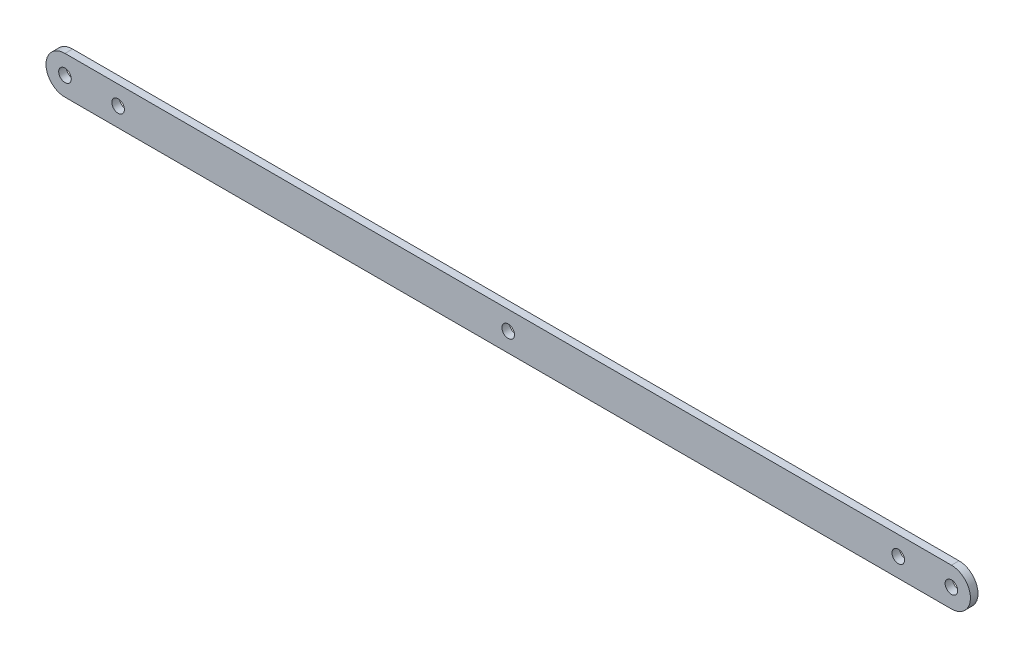
SolidWorks part; units mm, degrees
ref_plane "Přední rovina" through (0, 0, 0) normal (0, 0, 1) x (1, 0, 0)
ref_plane "Horní rovina" through (0, 0, 0) normal (0, 1, 0) x (1, 0, 0)
ref_plane "Pravá rovina" through (0, 0, 0) normal (1, 0, 0) x (0, 0, -1)
sketch "Skica1" plane through (0, 0, 0) normal (0, 0, 1) x (1, 0, 0)
  line L0 (0, 12.5) -> (584, 12.5)
  line L1 (0, -12.5) -> (584, -12.5)
  line L2 (0, 12.5) -> (0, -12.5) construction
  line L3 (584, -12.5) -> (584, 12.5) construction
  line L4 (-12.5, 0) -> (596.5, 0) construction
  line L5 (35, 4.15) -> (35, -4.15) construction
  line L6 (292, 4.15) -> (292, -4.15) construction
  line L7 (549, 4.15) -> (549, -4.15) construction
  arc A0 (0, 12.5) -> (0, -12.5) centre (0, 0) ccw
  arc A1 (584, 12.5) -> (584, -12.5) centre (584, 0) cw
  circle A2 centre (0, 0) radius 4.15
  circle A3 centre (584, 0) radius 4.15
  circle A4 centre (35, 0) radius 4.15
  circle A5 centre (292, 0) radius 4.15
  circle A6 centre (549, 0) radius 4.15
  dimension "D3" = 8.3
  dimension "D4" = 8.3
  dimension "D8" = 8.3
  dimension "D9" = 8.3
  dimension "D10" = 8.3
  dimension "D1" = 25
  dimension "D2" = 35
  dimension "D5" = 35
  dimension "D6" = 257
  dimension "D7" = 257
extrude "Přidat vysunutím1" add sketch "Skica1" along normal blind 5
